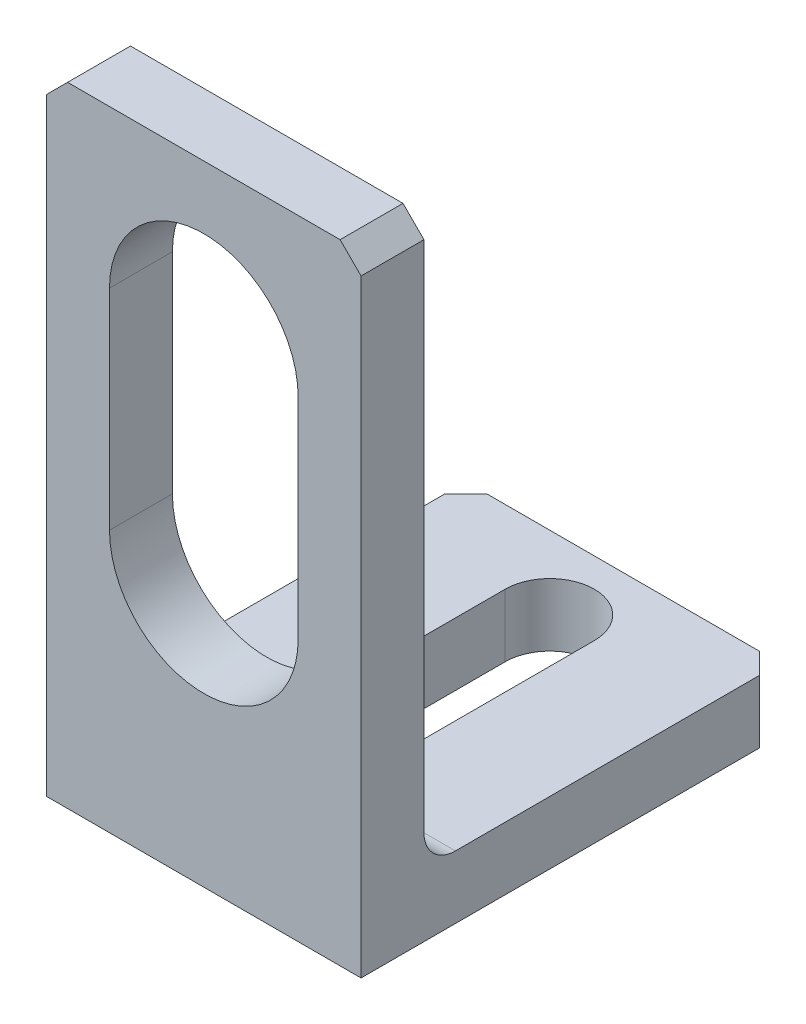
SolidWorks part; units mm, degrees
ref_plane "Front Plane" through (0, 0, 0) normal (0, 0, 1) x (1, 0, 0)
ref_plane "Top Plane" through (0, 0, 0) normal (0, 1, 0) x (1, 0, 0)
ref_plane "Right Plane" through (0, 0, 0) normal (1, 0, 0) x (0, 0, -1)
sketch "Sketch1" plane through (0, 0, 0) normal (0, 0, 1) x (1, 0, 0)
  line L0 (0, -552.4946) -> (0, 27072.2349) construction
  line L1 (-552.4946, 0) -> (27072.2349, 0) construction
  line L2 (0, 45) -> (0, 25) construction
  line L3 (-15, 60) -> (15, 60)
  line L4 (-15, 60) -> (-15, 0)
  line L5 (-15, 0) -> (15, 0)
  line L6 (15, 60) -> (15, 0)
  line L7 (-15, 60) -> (15, 0) construction
  line L8 (-15, 0) -> (15, 60) construction
  line L9 (9, 45) -> (9, 25)
  line L10 (-9, 45) -> (-9, 25)
  arc A0 (9, 45) -> (-9, 45) centre (0, 45) ccw
  arc A1 (-9, 25) -> (9, 25) centre (0, 25) ccw
  point P4 (0, 30)
  point P12 (0, 35)
  point P17 (0, 45.7288)
  dimension "D1" = 30
  dimension "D2" = 60
  dimension "D3" = 18
  dimension "D4" = 20
  dimension "D5" = 35
extrude "Boss-Extrude1" add sketch "Sketch1" along normal mid plane 6
sketch "Sketch3" plane through (0, 0, 0) normal (0, 1, 0) x (1, 0, 0)
  line L0 (0, -1000) -> (0, 49000) construction
  line L1 (15, -3) -> (15, 3) construction
  line L2 (-15, 3) -> (15, 3)
  line L3 (-15, 3) -> (-15, 37)
  line L4 (-15, 37) -> (15, 37)
  line L5 (15, 3) -> (15, 37)
  line L6 (15, -3) -> (-15, -3) construction
  line L7 (0, 30) -> (0, 12) construction
  line L8 (4.25, 30) -> (4.25, 12)
  line L9 (-4.25, 30) -> (-4.25, 12)
  arc A0 (4.25, 30) -> (-4.25, 30) centre (0, 30) ccw
  arc A1 (-4.25, 12) -> (4.25, 12) centre (0, 12) ccw
  point P14 (0, 21)
  dimension "D1" = 40
  dimension "D2" = 8.5
  dimension "D3" = 18
  dimension "D4" = 24
extrude "Boss-Extrude2" add sketch "Sketch3" along normal blind 6
fillet "Fillet1" radius 3 1 edges at (0, 6, -3)
chamfer "Chamfer1" distance 2 angle 45 4 edges at (-15, 3, -37) (15, 3, -37) (15, 60, 0) (-15, 60, 0)
